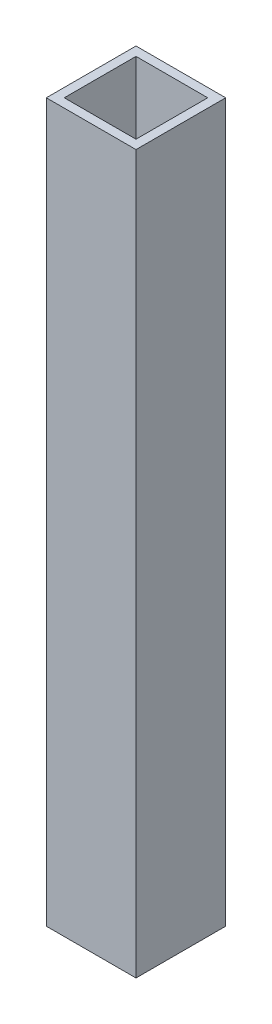
SolidWorks part; units mm, degrees
ref_plane "前视基准面" through (0, 0, 0) normal (0, 0, 1) x (1, 0, 0)
ref_plane "上视基准面" through (0, 0, 0) normal (0, 1, 0) x (1, 0, 0)
ref_plane "右视基准面" through (0, 0, 0) normal (1, 0, 0) x (0, 0, -1)
ref_plane "基准面4" through (0, -80, 0) normal (0, -1, 0) x (1, 0, 0)
sketch "草图1" plane through (0, -80, 0) normal (0, -1, 0) x (1, 0, 0)
  line L0 (25, -5) -> (25, 5)
  line L1 (25, 5) -> (15, 5)
  line L2 (15, 5) -> (15, -5)
  line L3 (15, -5) -> (25, -5)
  line L4 (24, 4) -> (24, -4)
  line L5 (24, -4) -> (16, -4)
  line L6 (16, -4) -> (16, 4)
  line L7 (16, 4) -> (24, 4)
extrude "凸台-拉伸1" add sketch "草图1" against normal blind 80
